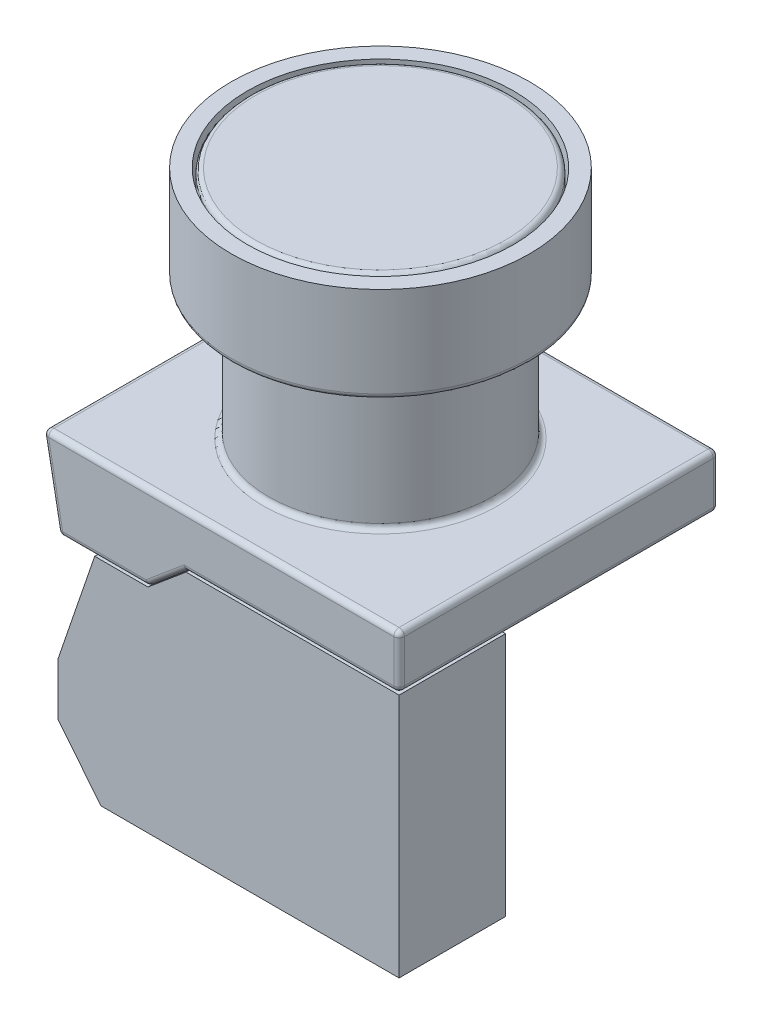
SolidWorks part; units mm, degrees
ref_plane "Front Plane" through (0, 0, 0) normal (0, 0, 1) x (1, 0, 0)
ref_plane "Top Plane" through (0, 0, 0) normal (0, 1, 0) x (1, 0, 0)
ref_plane "Right Plane" through (0, 0, 0) normal (1, 0, 0) x (0, 0, -1)
sketch "Sketch1" plane through (0, 0, 0) normal (0, 0, 1) x (1, 0, 0)
  line L0 (0, 0) -> (-4, 5)
  line L1 (8, 23) -> (28, 23)
  line L2 (-4, 10) -> (-4, 5)
  line L3 (0, 0) -> (28, 0)
  line L4 (28, 23) -> (28, 0)
  line L7 (-4, 10) -> (-0.5764, 20)
  line L8 (-0.5764, 20) -> (4.4236, 20)
  line L9 (4.4236, 20) -> (8, 23)
  dimension "D1" = 32
  dimension "D2" = 23
  dimension "D3" = 20
  dimension "D4" = 5
  dimension "D5" = 5
  dimension "D6" = 5
  dimension "D7" = 20
  dimension "D8" = 28
extrude "Boss-Extrude1" add sketch "Sketch1" along normal blind 10
sketch "Sketch3" plane through (0, 0, 10) normal (0, 0, 1) x (1, 0, 0)
  line L0 (28, 23) -> (8, 23)
  line L1 (8, 23) -> (4.4236, 20)
  line L2 (4.4236, 20) -> (-0.5764, 20)
  line L3 (-0.5764, 20) -> (-4, 20)
  line L4 (-4, 20) -> (-5.5, 28)
  line L5 (-5.5, 28) -> (28, 28)
  line L6 (28, 28) -> (28, 23)
  dimension "D1" = 8
  dimension "D2" = 1.5
extrude "Boss-Extrude2" add sketch "Sketch3" against normal blind 30 separate body
sketch "Sketch4" plane through (0, 28, 0) normal (0, 1, 0) x (1, 0, 0)
  line L0 (-5.5, 5) -> (28, 5) construction
  line L1 (-5.5, 20) -> (-5.5, -10) construction
  line L2 (28, 20) -> (28, -10) construction
  line L3 (11.25, 20) -> (11.25, -10) construction
  line L4 (28, 20) -> (-5.5, 20) construction
  line L5 (28, -10) -> (-5.5, -10) construction
  circle A0 centre (11.25, 5) radius 10.5
  dimension "D1" = 21
extrude "Boss-Extrude3" add sketch "Sketch4" along normal blind 13
sketch "Sketch5" plane through (0, 41, 0) normal (0, 1, 0) x (1, 0, 0)
  circle A0 centre (11.25, 5) radius 14
  dimension "D1" = 28
extrude "Boss-Extrude4" add sketch "Sketch5" along normal blind 9
sketch "Sketch6" plane through (0, 50, 0) normal (0, 1, 0) x (1, 0, 0)
  circle A0 centre (11.25, 5) radius 12.5
  dimension "D1" = 25
extrude "Cut-Extrude1" cut sketch "Sketch6" against normal blind 5
sketch "Sketch7" plane through (0, 45, 0) normal (0, 1, 0) x (1, 0, 0)
  circle A0 centre (11.25, 5) radius 12.25
  dimension "D1" = 24.5
extrude "Boss-Extrude5" add sketch "Sketch7" along normal blind 5
fillet "Fillet1" radius 0.5 1 edges at (11.25, 50, 7.25)
fillet "Fillet2" radius 0.5 20 edges at (-4, 20, -5) (-5.5, 28, -5) (11.25, 28, -20) (-4.75, 24, -20) (0.2118, 20, -20) (6.2118, 21.5, -20) (18, 23, -20) (18, 23, 10) (6.2118, 21.5, 10) (0.2118, 20, 10) (-4.75, 24, 10) (11.25, 28, 10) (28, 28, -5) (28, 25.5, -20) (28, 23, -5) (28, 25.5, 10) (4.4236, 20, -5) (11.25, 41, 5.5) (11.25, 28, 5.5) (11.25, 41, 9)
